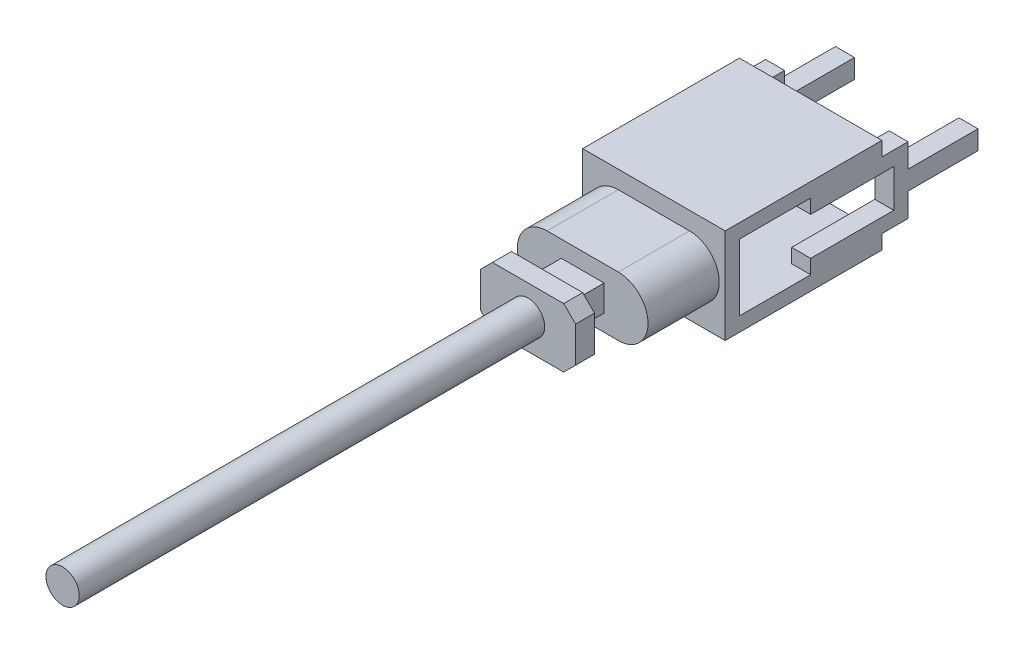
SolidWorks part; units mm, degrees
ref_plane "前视基准面" through (0, 0, 0) normal (0, 0, 1) x (1, 0, 0)
ref_plane "上视基准面" through (0, 0, 0) normal (0, 1, 0) x (1, 0, 0)
ref_plane "右视基准面" through (0, 0, 0) normal (1, 0, 0) x (0, 0, -1)
sketch "草图1" plane through (0, 0, 0) normal (0, 0, 1) x (1, 0, 0)
  circle A0 centre (0, 0) radius 7
extrude "凸台-拉伸1" add sketch "草图1" along normal blind 160 and the other way blind 36
sketch "草图2" plane through (0, 0, -36) normal (0, 0, -1) x (-1, 0, 0)
  line L0 (15, 12.5) -> (20, 7.5)
  line L1 (-20, 12.5) -> (20, 12.5)
  line L2 (-20, 12.5) -> (-20, -12.5)
  line L3 (-20, -12.5) -> (20, -12.5)
  line L4 (20, 12.5) -> (20, -12.5)
  line L5 (-20, 12.5) -> (20, -12.5) construction
  line L6 (-20, -12.5) -> (20, 12.5) construction
  line L7 (-15, 12.5) -> (-20, 7.5)
  line L8 (-20, -7.5) -> (-15, -12.5)
  line L9 (-15, -12.5) -> (15, -12.5)
  line L10 (15, -12.5) -> (20, -7.5)
  point P0 (0, 0)
  circle M1 centre (0, 0) radius 7
  dimension "D1" = 25
  dimension "D2" = 40
  dimension "D3" = 5
  dimension "D4" = 5
  dimension "D5" = 5
  dimension "D6" = 5
  dimension "D7" = 5
  dimension "D8" = 5
  dimension "D9" = 5
  dimension "D10" = 5
extrude "凸台-拉伸2" add sketch "草图2" along normal blind 8 contours L3 L10 L4 L0 L1 L7 L2 L8 M1 | M1
sketch "草图3" plane through (0, 0, -44) normal (0, 0, -1) x (-1, 0, 0)
  line L1 (9, 5.5) -> (-9, 5.5)
  line L2 (9, 5.5) -> (9, -5.5)
  line L3 (9, -5.5) -> (-9, -5.5)
  line L4 (-9, 5.5) -> (-9, -5.5)
  line L5 (9, 5.5) -> (-9, -5.5) construction
  line L6 (9, -5.5) -> (-9, 5.5) construction
  point P0 (0, 0)
  dimension "D1" = 18
  dimension "D2" = 11
extrude "凸台-拉伸3" add sketch "草图3" along normal blind 15
sketch "草图4" plane through (0, 0, -59) normal (0, 0, -1) x (-1, 0, 0)
  line L1 (15, 12.5) -> (-15, 12.5)
  line L2 (15, 12.5) -> (15, -12.5)
  line L3 (15, -12.5) -> (-15, -12.5)
  line L4 (-15, 12.5) -> (-15, -12.5)
  line L5 (15, 12.5) -> (-15, -12.5) construction
  line L6 (15, -12.5) -> (-15, 12.5) construction
  circle A0 centre (15, 0) radius 12.5
  circle A1 centre (-15, 0) radius 12.5
  point P0 (0, 0)
  line M1 (-9, 5.5) -> (-9, -5.5)
  line M2 (-9, -5.5) -> (9, -5.5)
  line M3 (9, -5.5) -> (9, 5.5)
  line M4 (9, 5.5) -> (-9, 5.5)
  dimension "D1" = 25
  dimension "D2" = 30
extrude "凸台-拉伸4" add sketch "草图4" along normal blind 30 contours L4 A1 | A1 L4 M4 M2 M1 | A1 M2 M4 M1 | A1 A0 M2 M4 | A0 M4 M2 M3 | L2 A0 M4 M3 M2 | L2 A0 | A1 L3 A0 M2 | A1 A0 L1 M4
sketch "草图5" plane through (0, 0, -89) normal (0, 0, -1) x (-1, 0, 0)
  line L1 (30, 20) -> (-30, 20)
  line L2 (30, 20) -> (30, -20)
  line L3 (30, -20) -> (-30, -20)
  line L4 (-30, 20) -> (-30, -20)
  line L5 (30, 20) -> (-30, -20) construction
  line L6 (30, -20) -> (-30, 20) construction
  point P0 (0, 0)
  dimension "D1" = 60
  dimension "D2" = 40
extrude "凸台-拉伸5" add sketch "草图5" along normal blind 6
sketch "草图6" plane through (0, 0, -95) normal (0, 0, -1) x (-1, 0, 0)
  line L0 (-30, 20) -> (-30, -20) construction
  line L1 (30, 20) -> (-30, 20)
  line L2 (30, 20) -> (30, 14)
  line L3 (30, 14) -> (-30, 14)
  line L4 (-30, 20) -> (-30, 14)
  line L5 (30, -20) -> (30, 20) construction
  line L6 (-30, -20) -> (30, -20)
  line L7 (-30, -20) -> (-30, -14)
  line L8 (-30, -14) -> (30, -14)
  line L9 (30, -20) -> (30, -14)
  dimension "D1" = 6
  dimension "D2" = 6
extrude "凸台-拉伸6" add sketch "草图6" along normal blind 60
sketch "草图7" plane through (-30, 0, 0) normal (-1, 0, 0) x (0, 0, 1)
  line L0 (-155, 14) -> (-95, 14) construction
  line L1 (-125, 14) -> (-160, 14)
  line L2 (-125, 14) -> (-125, 8)
  line L3 (-125, 8) -> (-160, 8)
  line L4 (-160, 14) -> (-160, 8)
  line L5 (-155, -14) -> (-95, -14) construction
  line L6 (-125, -14) -> (-160, -14)
  line L7 (-125, -14) -> (-125, -8)
  line L8 (-125, -8) -> (-160, -8)
  line L9 (-160, -14) -> (-160, -8)
  line L11 (-160, 14) -> (-166, 14)
  line L12 (-160, 14) -> (-160, -14)
  line L13 (-160, -14) -> (-166, -14)
  line L14 (-166, 14) -> (-166, -14)
  line L15 (-166, 0) -> (-195.4559, 0)
  line L16 (-166, 0) -> (-166, 4)
  line L17 (-166, 4) -> (-195.4559, 4)
  line L18 (-195.4559, 0) -> (-195.4559, 4)
  line L19 (-166, 0) -> (-195.4559, 0)
  line L20 (-166, 0) -> (-166, -4)
  line L21 (-166, -4) -> (-195.4559, -4)
  line L22 (-195.4559, 0) -> (-195.4559, -4)
  line M4 (-155, 14) -> (-95, 14)
  line M6 (-95, -14) -> (-155, -14)
  dimension "D1" = 6
  dimension "D2" = 6
  dimension "D3" = 6
  dimension "D4" = 35
  dimension "D5" = 4
  dimension "D6" = 4
extrude "凸台-拉伸7" add sketch "草图7" against normal blind 8 contours L1 L4 L3 L2 M4 | L9 L6 L7 L8 M6 | L11 L14 L13 L9 L12 L4 | L15 L22 L21 L14 | L18 L15 L14 L17
pattern_linear "阵列(线性)1" count 2 spacing 52 along (1, 0, 0) of "凸台-拉伸7"
